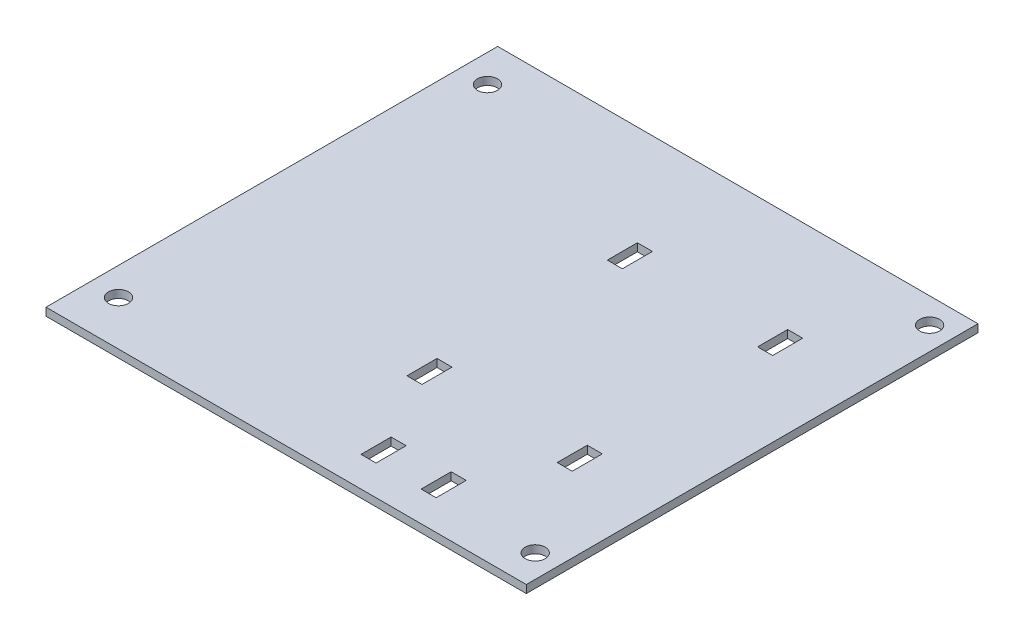
SolidWorks part; units mm, degrees
other "DetailItem3"
material "ABS"
ref_plane "Front Plane" through (0, 0, 0) normal (0, 0, 1) x (1, 0, 0)
ref_plane "Top Plane" through (0, 0, 0) normal (0, 1, 0) x (1, 0, 0)
ref_plane "Right Plane" through (0, 0, 0) normal (1, 0, 0) x (0, 0, -1)
sketch "Sketch1" plane through (0, 0, 0) normal (0, 1, 0) x (1, 0, 0)
  line L1 (-32.2441, 108.719) -> (64.6459, 108.719)
  line L2 (-32.2441, 108.719) -> (-32.2441, 18.549)
  line L3 (-32.2441, 18.549) -> (64.6459, 18.549)
  line L4 (64.6459, 108.719) -> (64.6459, 18.549)
  dimension "D1" = 96.89
  dimension "D2" = 90.17
extrude "PCB" add sketch "Sketch1" along normal blind 1.57
sketch "Sketch2" plane through (0, 1.57, 0) normal (0, 1, 0) x (1, 0, 0)
  line L0 (64.6459, 18.549) -> (64.6459, 108.719) construction
  line L1 (-32.2441, 18.549) -> (64.6459, 18.549) construction
  circle A0 centre (59.5659, 24.899) radius 2
  circle A1 centre (-26.1641, 27.439) radius 2
  circle A2 centre (-26.1641, 101.099) radius 2
  circle A3 centre (59.5659, 103.639) radius 2
  dimension "D3" = 4
  dimension "D6" = 4
  dimension "D11" = 4
  dimension "D12" = 4
  dimension "D1" = 5.08
  dimension "D2" = 6.35
  dimension "D4" = 90.81
  dimension "D5" = 8.89
  dimension "D7" = 90.81
  dimension "D8" = 5.08
  dimension "D9" = 85.09
  dimension "D10" = 82.55
extrude "M3 Mounting Holes" cut sketch "Sketch2" against normal blind 1.57
sketch "Sketch5" plane through (0, 1.57, 0) normal (0, 1, 0) x (1, 0, 0)
  line L0 (64.6459, 108.719) -> (-32.2441, 108.719) construction
  line L1 (-32.2441, 18.549) -> (-31.7441, 18.549)
  line L2 (-32.2441, 18.549) -> (-32.2441, 108.719)
  line L3 (-32.2441, 108.719) -> (-31.7441, 108.719)
  line L4 (-31.7441, 18.549) -> (-31.7441, 108.719)
  line L5 (-32.2441, 18.549) -> (64.6459, 18.549) construction
  line L6 (64.6459, 108.719) -> (64.1459, 108.719)
  line L7 (64.6459, 108.719) -> (64.6459, 18.549)
  line L8 (64.6459, 18.549) -> (64.1459, 18.549)
  line L9 (64.1459, 108.719) -> (64.1459, 18.549)
  dimension "D1" = 0.5
  dimension "D2" = 0.5
extrude "Cut-Extrude1" cut sketch "Sketch5" against normal through all
sketch "Sketch6" plane through (0, 1.57, 0) normal (0, 1, 0) x (1, 0, 0)
  line L1 (16.1459, 88.719) -> (19.1459, 88.719)
  line L2 (16.1459, 88.719) -> (16.1459, 82.719)
  line L3 (16.1459, 82.719) -> (19.1459, 82.719)
  line L4 (19.1459, 88.719) -> (19.1459, 82.719)
  line L5 (46.1459, 88.719) -> (49.1459, 88.719)
  line L6 (46.1459, 88.719) -> (46.1459, 82.719)
  line L7 (46.1459, 82.719) -> (49.1459, 82.719)
  line L8 (49.1459, 88.719) -> (49.1459, 82.719)
  line L9 (16.1459, 48.719) -> (19.1459, 48.719)
  line L10 (16.1459, 48.719) -> (16.1459, 42.719)
  line L11 (16.1459, 42.719) -> (19.1459, 42.719)
  line L12 (19.1459, 48.719) -> (19.1459, 42.719)
  line L13 (46.1459, 48.719) -> (49.1459, 48.719)
  line L14 (46.1459, 48.719) -> (46.1459, 42.719)
  line L15 (46.1459, 42.719) -> (49.1459, 42.719)
  line L16 (49.1459, 48.719) -> (49.1459, 42.719)
  line L17 (64.1459, 108.719) -> (-31.7441, 108.719) construction
  line L18 (64.1459, 108.719) -> (64.1459, 18.549) construction
  line L19 (-31.7441, 18.549) -> (64.1459, 18.549) construction
  line L20 (25.1459, 30.549) -> (28.1459, 30.549)
  line L21 (25.1459, 30.549) -> (25.1459, 24.549)
  line L22 (25.1459, 24.549) -> (28.1459, 24.549)
  line L23 (28.1459, 30.549) -> (28.1459, 24.549)
  line L24 (37.1459, 30.549) -> (40.1459, 30.549)
  line L25 (37.1459, 30.549) -> (37.1459, 24.549)
  line L26 (37.1459, 24.549) -> (40.1459, 24.549)
  line L27 (40.1459, 30.549) -> (40.1459, 24.549)
  dimension "D1" = 3
  dimension "D2" = 6
  dimension "D3" = 6
  dimension "D4" = 3
  dimension "D5" = 20
  dimension "D6" = 20
  dimension "D7" = 27
  dimension "D8" = 15
  dimension "D9" = 6
  dimension "D10" = 6
  dimension "D11" = 3
  dimension "D12" = 3
  dimension "D13" = 15
  dimension "D14" = 27
  dimension "D15" = 40
  dimension "D16" = 40
  dimension "D17" = 3
  dimension "D18" = 6
  dimension "D19" = 6
  dimension "D20" = 3
  dimension "D21" = 6
  dimension "D22" = 6
  dimension "D23" = 6
  dimension "D24" = 6
extrude "ZipTie Holds" cut sketch "Sketch6" against normal blind 10
